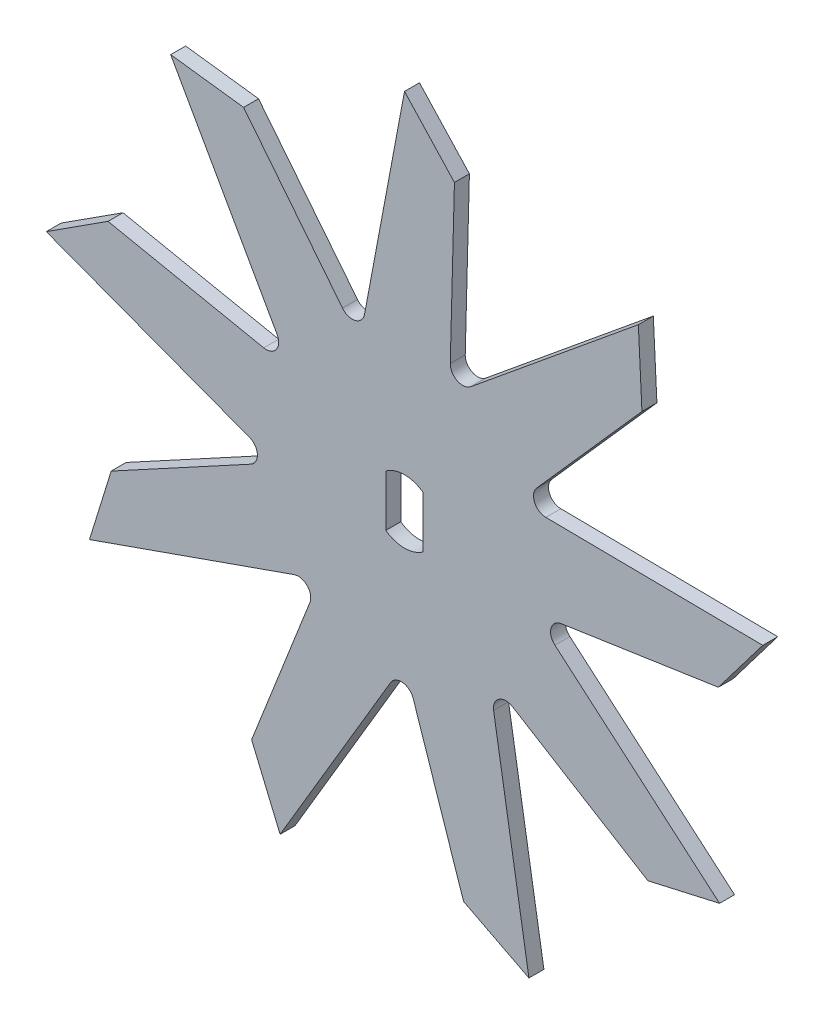
SolidWorks part; units mm, degrees
ref_plane "Plan de face" through (0, 0, 0) normal (0, 0, 1) x (1, 0, 0)
ref_plane "Plan de dessus" through (0, 0, 0) normal (0, 1, 0) x (1, 0, 0)
ref_plane "Plan de droite" through (0, 0, 0) normal (1, 0, 0) x (0, 0, -1)
sketch "Esquisse1" plane through (0, 0, 0) normal (0, 0, 1) x (1, 0, 0)
  line L2 (0, 145.75) -> (0, 0) construction
  line L19 (-7.5, 10.3108) -> (-7.5, -10.3108)
  line L20 (7.5, 10.3108) -> (7.5, -10.3108)
  line L21 (-16.0244, 60.3224) -> (0, 145.75)
  line L22 (18.0416, 49.5688) -> (0, 145.75) construction
  line L23 (0, 145.75) -> (20, 124.1494)
  line L24 (20, 124.1494) -> (18.3288, 60.5062)
  line L25 (93.6863, 111.651) -> (95.1226, 82.2482)
  line L26 (26.4991, 56.5099) -> (93.6863, 111.651)
  line L27 (95.1226, 82.2482) -> (52.9333, 34.5689)
  line L28 (143.5357, 25.3092) -> (125.7362, 1.8622)
  line L29 (56.6234, 26.2558) -> (143.5357, 25.3092)
  line L30 (125.7362, 1.8622) -> (62.7697, -7.5435)
  line L31 (126.2232, -72.875) -> (97.5165, -79.3952)
  line L32 (60.2529, -16.2837) -> (126.2232, -72.875)
  line L33 (97.5165, -79.3952) -> (43.2355, -46.1263)
  line L34 (49.8494, -136.9602) -> (23.6677, -123.5026)
  line L35 (35.6895, -51.2038) -> (49.8494, -136.9602)
  line L36 (23.6677, -123.5026) -> (3.4709, -63.126)
  line L37 (-49.8494, -136.9602) -> (-61.2554, -109.8218)
  line L38 (-5.5735, -62.1652) -> (-49.8494, -136.9602)
  line L39 (-61.2554, -109.8218) -> (-37.9177, -50.5884)
  line L40 (-126.2232, -72.875) -> (-117.5165, -44.7542)
  line L41 (-44.2285, -44.0387) -> (-126.2232, -72.875)
  line L42 (-117.5165, -44.7542) -> (-61.5643, -14.3799)
  line L43 (-143.5357, 25.3092) -> (-118.7903, 41.2545)
  line L44 (-62.1886, -5.3061) -> (-143.5357, 25.3092)
  line L45 (-118.7903, 41.2545) -> (-56.4042, 28.5571)
  line L46 (-93.6863, 111.651) -> (-64.4808, 107.9597)
  line L47 (-51.0499, 35.9093) -> (-93.6863, 111.651)
  line L48 (-64.4808, 107.9597) -> (-24.852, 58.1319)
  circle A0 centre (0, 0) radius 52.75 construction
  circle A1 centre (0, 0) radius 145.75 construction
  arc A11 (-7.5, 10.3108) -> (-7.5, -10.3108) centre (0, 0) ccw construction
  arc A12 (7.5, 10.3108) -> (-7.5, 10.3108) centre (0, 0) ccw
  arc A13 (7.5, -10.3108) -> (7.5, 10.3108) centre (0, 0) ccw construction
  arc A14 (-7.5, -10.3108) -> (7.5, -10.3108) centre (0, 0) ccw
  circle A15 centre (0, 0) radius 125.75 construction
  arc A16 (-56.4042, 28.5571) -> (-51.0499, 35.9093) centre (-55.407, 33.4567) ccw
  arc A17 (-61.5643, -14.3799) -> (-62.1886, -5.3061) centre (-63.9497, -9.9856) ccw
  arc A18 (-37.9177, -50.5884) -> (-44.2285, -44.0387) centre (-42.5697, -48.7556) ccw
  arc A19 (3.4709, -63.126) -> (-5.5735, -62.1652) centre (-1.2708, -64.7122) ccw
  arc A20 (43.2355, -46.1263) -> (35.6895, -51.2038) centre (40.6227, -50.3893) ccw
  arc A21 (62.7697, -7.5435) -> (60.2529, -16.2837) centre (63.5084, -12.4887) ccw
  arc A22 (52.9333, 34.5689) -> (56.6234, 26.2558) centre (56.6778, 31.2555) ccw
  arc A23 (-16.0244, 60.3224) -> (-24.852, 58.1319) centre (-20.9387, 61.2442) cw
  arc A24 (18.3288, 60.5062) -> (26.4991, 56.5099) centre (23.327, 60.3749) ccw
  point P34 (0, 0)
  point P49 (0, 0)
  point P56 (-18.0416, 49.5688)
  dimension "D1" = 133
  dimension "D2" = 40
  dimension "D4" = 20
  dimension "D5" = 25.5
  dimension "D3" = 20
  dimension "D8" = 5
  dimension "D6" = 15
  dimension "D7" = 9
extrude "Boss.-Extru.1" add sketch "Esquisse1" along normal blind 6
